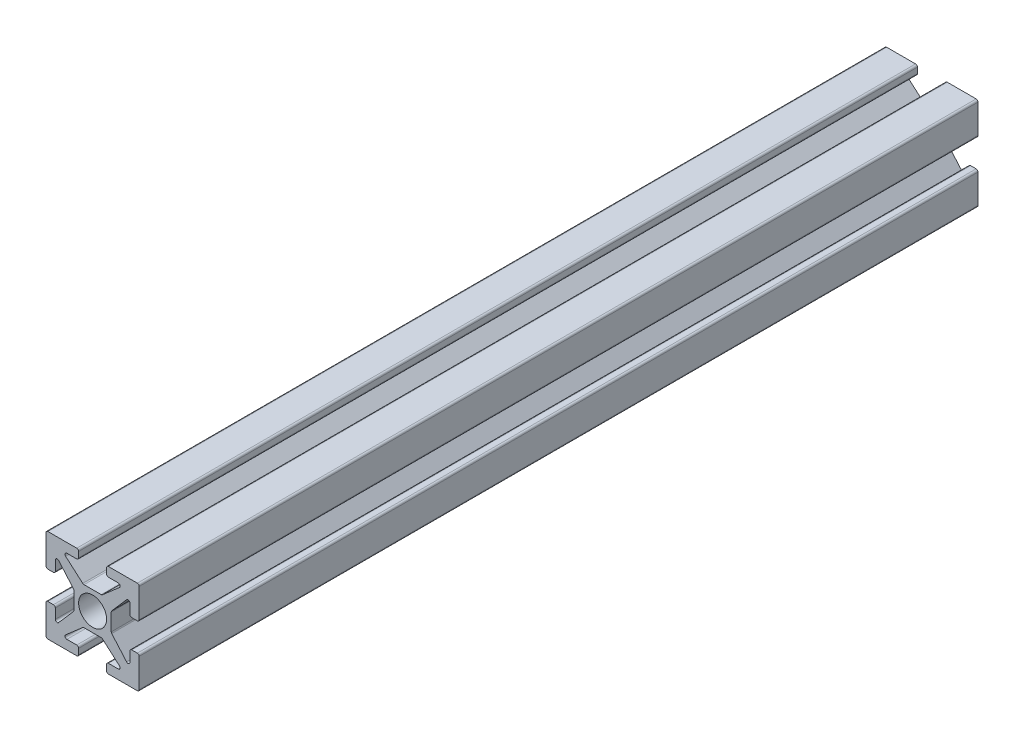
SolidWorks part; units mm, degrees
ref_plane "Front Plane" through (0, 0, 0) normal (0, 0, 1) x (1, 0, 0)
ref_plane "Top Plane" through (0, 0, 0) normal (0, 1, 0) x (1, 0, 0)
ref_plane "Right Plane" through (0, 0, 0) normal (1, 0, 0) x (0, 0, -1)
ref_plane "Plane1" through (0, 5, 0) normal (0, 1, 0) x (1, 0, 0)
sketch "Sketch1" plane through (0, 5, 0) normal (0, 1, 0) x (1, 0, 0)
  line L0 (5, 45) -> (-5, 45)
  line L1 (-5, 45) -> (-5, -45)
  line L2 (-5, -45) -> (5, -45)
  line L3 (5, -45) -> (5, 45)
  point P4 (0, 0)
  point P5 (-5, 0)
  dimension "D1" = 90
  dimension "D2" = 10
extrude "Boss-Extrude1" add sketch "Sketch1" against normal blind 10
sketch "Sketch2" plane through (0, 0, 45) normal (0, 0, 1) x (1, 0, 0)
  line L0 (5, 1.5) -> (4, 1.5)
  line L1 (4, 1.5) -> (4, 2.7593)
  line L2 (3.6493, 2.8908) -> (2, 1)
  line L3 (2, 1) -> (2, -1)
  line L4 (2, -1) -> (3.6493, -2.8908)
  line L5 (4, -2.7593) -> (4, -1.5)
  line L6 (4, -1.5) -> (5, -1.5)
  line L7 (5, -1.5) -> (5, 1.5)
  arc A0 (4, 2.7593) -> (3.6493, 2.8908) centre (3.8, 2.7593) ccw
  arc A1 (3.6493, -2.8908) -> (4, -2.7593) centre (3.8, -2.7593) ccw
extrude "Cut-Extrude1" cut sketch "Sketch2" against normal through all
sketch "Sketch3" plane through (0, 0, 45) normal (0, 0, 1) x (1, 0, 0)
  line L0 (1.5, -5) -> (1.5, -4)
  line L1 (1.5, -4) -> (2.7593, -4)
  line L2 (2.8908, -3.6493) -> (1, -2)
  line L3 (1, -2) -> (-1, -2)
  line L4 (-1, -2) -> (-2.8908, -3.6493)
  line L5 (-2.7593, -4) -> (-1.5, -4)
  line L6 (-1.5, -4) -> (-1.5, -5)
  line L7 (-1.5, -5) -> (1.5, -5)
  arc A0 (2.7593, -4) -> (2.8908, -3.6493) centre (2.7593, -3.8) ccw
  arc A1 (-2.8908, -3.6493) -> (-2.7593, -4) centre (-2.7593, -3.8) ccw
extrude "Cut-Extrude2" cut sketch "Sketch3" against normal through all
sketch "Sketch4" plane through (0, 0, 45) normal (0, 0, 1) x (1, 0, 0)
  line L0 (-5, -1.5) -> (-4, -1.5)
  line L1 (-4, -1.5) -> (-4, -2.7593)
  line L2 (-3.6493, -2.8908) -> (-2, -1)
  line L3 (-2, -1) -> (-2, 1)
  line L4 (-2, 1) -> (-3.6493, 2.8908)
  line L5 (-4, 2.7593) -> (-4, 1.5)
  line L6 (-4, 1.5) -> (-5, 1.5)
  line L7 (-5, 1.5) -> (-5, -1.5)
  arc A0 (-4, -2.7593) -> (-3.6493, -2.8908) centre (-3.8, -2.7593) ccw
  arc A1 (-3.6493, 2.8908) -> (-4, 2.7593) centre (-3.8, 2.7593) ccw
extrude "Cut-Extrude3" cut sketch "Sketch4" against normal through all
sketch "Sketch5" plane through (0, 0, 45) normal (0, 0, 1) x (1, 0, 0)
  line L0 (-1.5, 5) -> (-1.5, 4)
  line L1 (-1.5, 4) -> (-2.7593, 4)
  line L2 (-2.8908, 3.6493) -> (-1, 2)
  line L3 (-1, 2) -> (1, 2)
  line L4 (1, 2) -> (2.8908, 3.6493)
  line L5 (2.7593, 4) -> (1.5, 4)
  line L6 (1.5, 4) -> (1.5, 5)
  line L7 (1.5, 5) -> (-1.5, 5)
  arc A0 (-2.7593, 4) -> (-2.8908, 3.6493) centre (-2.7593, 3.8) ccw
  arc A1 (2.8908, 3.6493) -> (2.7593, 4) centre (2.7593, 3.8) ccw
extrude "Cut-Extrude4" cut sketch "Sketch5" against normal through all
sketch "Sketch6" plane through (0, 0, 0) normal (0, 1, 0) x (1, 0, 0)
  line L0 (1.5, 37) -> (1.25, 36.8498)
  line L1 (0, 45) -> (0, -45)
  line L2 (0, -45) -> (1.5, -45)
  line L3 (1.5, -45) -> (1.5, -37)
  line L4 (1.5, -37) -> (1.25, -36.8498)
  line L5 (1.25, -36.8498) -> (1.25, 36.8498)
  line L6 (1.5, 45) -> (1.5, 37)
  line L7 (0, 45) -> (1.5, 45)
  line L8 (0, 45) -> (0, -45) construction
  line L9 (-1, -45) -> (1, -45) construction
  line L10 (0, 0) -> (7.2534, 0) construction
  point P6 (1.25, 0)
  dimension "D1" = 1.25
  dimension "D2" = 1.5
  dimension "D3" = 121
  dimension "D4" = 8
revolve "Cut-Revolve1" cut sketch "Sketch6" angle 360 about L8
fillet "Fillet1" radius 0.2 28 edges at (-5, 1.5, 0) (1.5, -5, 0) (-5, -5, 0) (-1.5, 4, 0) (2, 1, 0) (-4, 1.5, 0) (-2, -1, 0) (-4, -1.5, 0) (-1, -2, 0) (-1.5, -4, 0) (5, -1.5, 0) (1.5, -4, 0) (-5, 5, 0) (4, -1.5, 0) (-2, 1, 0) (4, 1.5, 0) (-5, -1.5, 0) (5, 1.5, 0) (-1.5, -5, 0) (5, 5, 0) (1, -2, 0) (1.5, 5, 0) (5, -5, 0) (1, 2, 0) (2, -1, 0) (-1, 2, 0) (1.5, 4, 0) (-1.5, 5, 0)
equation "\"length\"=90"
equation "\"D1@Sketch1\"=\"length\""
